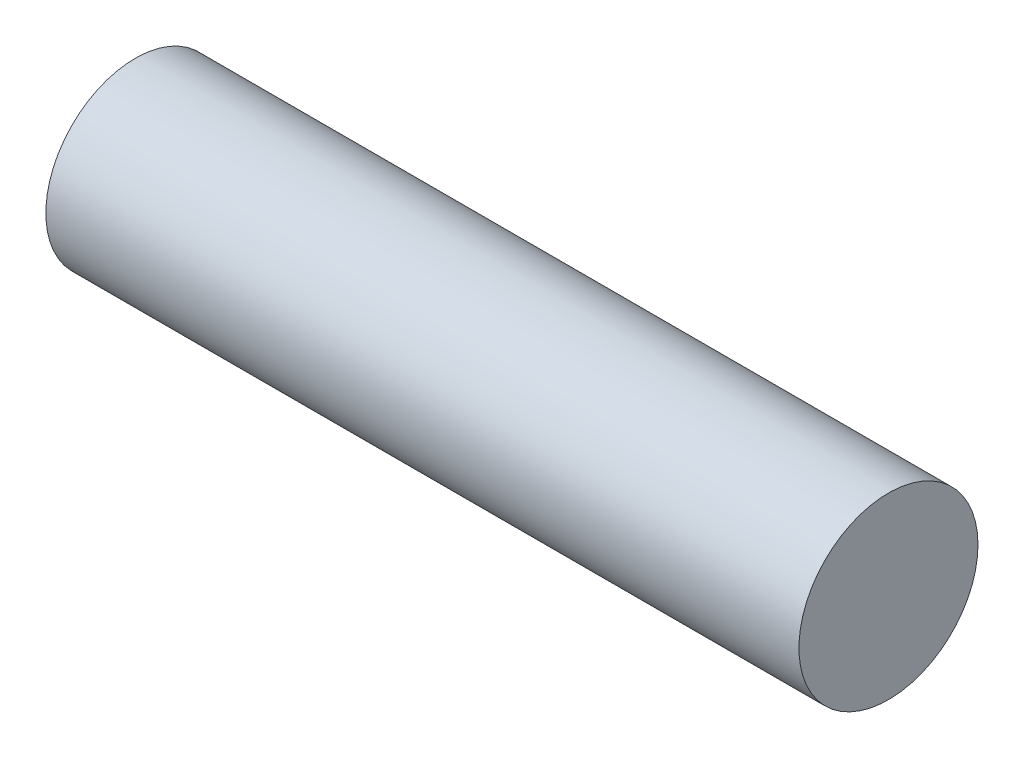
SolidWorks part; units mm, degrees
ref_plane "Front Plane" through (0, 0, 0) normal (0, 0, 1) x (1, 0, 0)
ref_plane "Top Plane" through (0, 0, 0) normal (0, 1, 0) x (1, 0, 0)
ref_plane "Right Plane" through (0, 0, 0) normal (1, 0, 0) x (0, 0, -1)
sketch "Sketch1" plane through (0, 0, 0) normal (1, 0, 0) x (0, 0, -1)
  circle A0 centre (0, 0) radius 10.75
  circle A1 centre (0, 0) radius 10
  dimension "D1" = 21.5
  dimension "D2" = 0.75
extrude "Boss-Extrude1" add sketch "Sketch1" along normal blind 89.43
sketch "Sketch2" plane through (89.43, 0, 0) normal (1, 0, 0) x (0, 0, -1)
  circle A0 centre (0, 0) radius 10.75 construction
  circle A1 centre (0, 0) radius 10.75
extrude "Boss-Extrude2" add sketch "Sketch2" along normal blind 1
